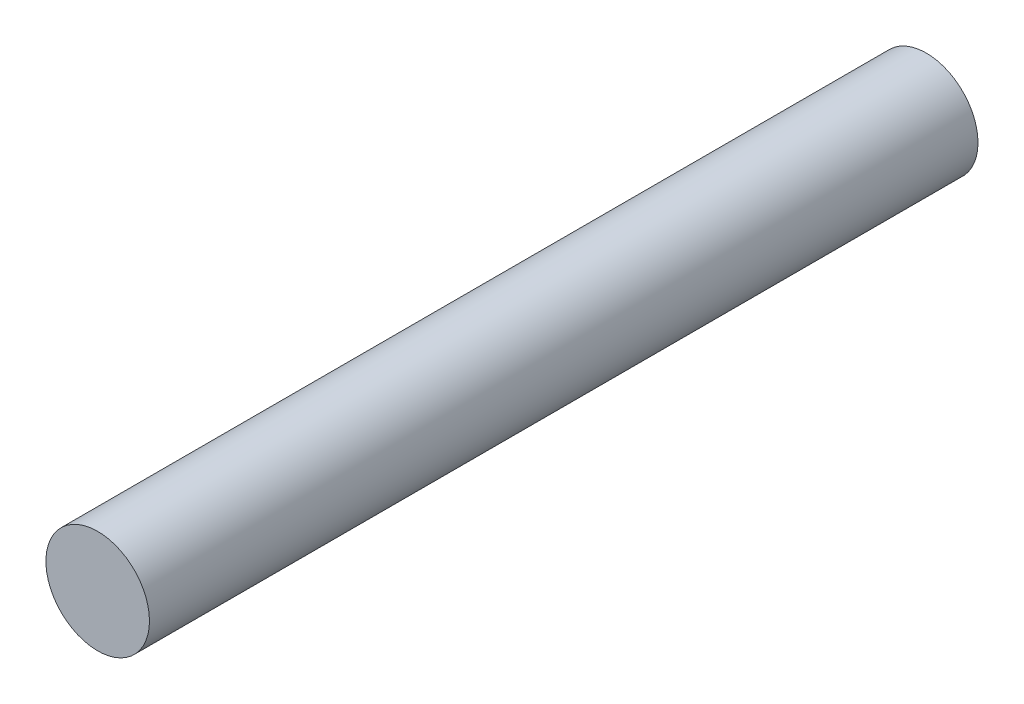
SolidWorks part; units mm, degrees
ref_plane "Front Plane" through (0, 0, 0) normal (0, 0, 1) x (1, 0, 0)
ref_plane "Top Plane" through (0, 0, 0) normal (0, 1, 0) x (1, 0, 0)
ref_plane "Right Plane" through (0, 0, 0) normal (1, 0, 0) x (0, 0, -1)
sketch "Sketch1" plane through (0, 0, 0) normal (0, 0, 1) x (1, 0, 0)
  circle A0 centre (0, 0) radius 2.5
  dimension "D1" = 5
extrude "Boss-Extrude1" add sketch "Sketch1" along normal blind 40
equation "\"shaft diameter\"=0.5"
equation "\"D1@Sketch1\"=\"shaft diameter\""
